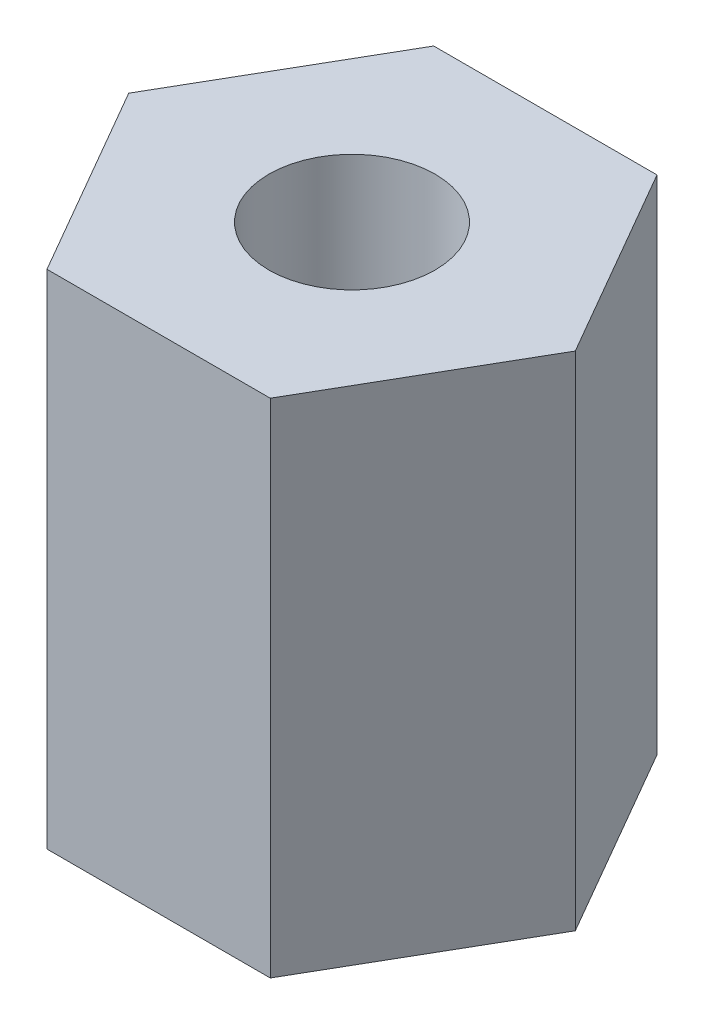
SolidWorks part; units mm, degrees
material "Silicone Rubber"
ref_plane "Front Plane" through (0, 0, 0) normal (0, 0, 1) x (1, 0, 0)
ref_plane "Top Plane" through (0, 0, 0) normal (0, 1, 0) x (1, 0, 0)
ref_plane "Right Plane" through (0, 0, 0) normal (1, 0, 0) x (0, 0, -1)
sketch "Sketch1" plane through (0, 0, 0) normal (0, 1, 0) x (1, 0, 0)
  line L0 (-2.935, 0) -> (2.935, 0) construction
  line L1 (-1.4675, 2.5418) -> (-2.935, 0)
  line L2 (-2.935, 0) -> (-1.4675, -2.5418)
  line L3 (-1.4675, -2.5418) -> (1.4675, -2.5418)
  line L4 (1.4675, -2.5418) -> (2.935, 0)
  line L5 (2.935, 0) -> (1.4675, 2.5418)
  line L6 (1.4675, 2.5418) -> (-1.4675, 2.5418)
  circle A0 centre (0, 0) radius 2.5418 construction
  dimension "D1" = 5.87
extrude "Boss-Extrude1" add sketch "Sketch1" along normal blind 6.6
sketch "Sketch2" plane through (0, 0, 0) normal (0, -1, 0) x (-1, 0, 0)
  circle A0 centre (0, 0) radius 1.0922
  dimension "D1" = 2.1844
extrude "Cut-Extrude1" cut sketch "Sketch2" against normal blind 6.6 contours A0
thread "Thread1" pitch 0.4536 start angle 0, offset 0, length 0, pitch 0.4536, diameter 2.1844
ref_plane "Plane1" through (-1.0922, 6.6, 0) normal (0, 0, 1) x (-1, 0, 0)
sketch "Thread Profile1" plane through (-1.0922, 6.6, 0) normal (0, 0, 1) x (-1, 0, 0)
  line L0 (0, 0) -> (0, 0.4536) construction
  line L11 (0, 0) -> (0, 0.3969)
  line L12 (0, 0.3969) -> (-0.2455, 0.2551)
  line L13 (-0.2455, 0.2551) -> (-0.2455, 0.1417)
  line L15 (-0.2455, 0.1417) -> (0, 0)
  line L17 (-0.2455, 0.1984) -> (0, 0.1984) construction
  point P2 (0, 0)
  dimension "Pitch" = 0.4536
  dimension "Profile_Angle" = 60
  dimension "Profile_Land" = 0.1134
  dimension "Profile_Height" = 0.2455
